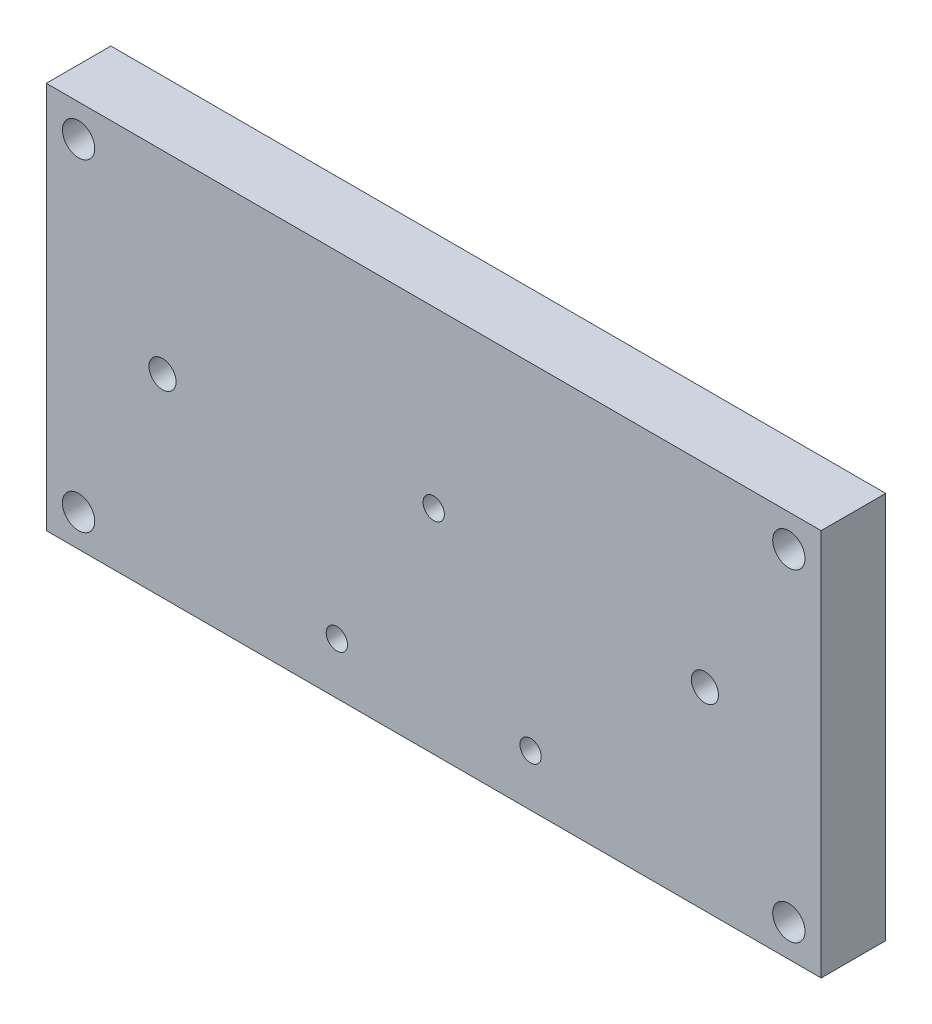
SolidWorks part; units mm, degrees
ref_plane "Ebene vorne" through (0, 0, 0) normal (0, 0, 1) x (1, 0, 0)
ref_plane "Ebene oben" through (0, 0, 0) normal (0, 1, 0) x (1, 0, 0)
ref_plane "Ebene rechts" through (0, 0, 0) normal (1, 0, 0) x (0, 0, -1)
sketch "Skizze1" plane through (0, 0, 0) normal (0, 0, 1) x (1, 0, 0)
  line L1 (-60, 30) -> (60, 30)
  line L2 (-60, 30) -> (-60, -30)
  line L3 (-60, -30) -> (60, -30)
  line L4 (60, 30) -> (60, -30)
  line L5 (-60, 30) -> (60, -30) construction
  line L6 (-60, -30) -> (60, 30) construction
  point P0 (0, 0)
  dimension "D1" = 120
  dimension "D2" = 60
extrude "Aufsatz-Linear austragen1" add sketch "Skizze1" along normal blind 10
sketch "Skizze2" plane through (0, 0, 10) normal (0, 0, 1) x (1, 0, 0)
  line L0 (-60, 30) -> (-60, -30) construction
  line L1 (55, -25) -> (-55, -25) construction
  line L2 (55, -25) -> (55, 25) construction
  line L3 (55, 25) -> (-55, 25) construction
  line L4 (-55, -25) -> (-55, 25) construction
  line L5 (55, -25) -> (-55, 25) construction
  line L6 (55, 25) -> (-55, -25) construction
  line L7 (-60, -30) -> (60, -30) construction
  point P0 (0, 0)
  point P7 (-55, 25)
  point P8 (55, 25)
  point P9 (55, -25)
  point P10 (-55, -25)
  dimension "D1" = 5
  dimension "D2" = 5
hole_wizard "M6 Gewindebohrung1" positions "Skizze3" profile "Skizze4" tap size "M6" standard "DIN" end condition through all
sketch "Skizze3" plane through (0, 0, 10) normal (0, 0, 1) x (1, 0, 0)
  point P0 (-55, -25)
  point P3 (-55, 25)
  point P6 (55, 25)
  point P9 (55, -25)
sketch "Skizze4" plane through (-55, -25, 10) normal (1, 0, 0) x (0, -1, 0)
  line L0 (0, 0) -> (0, 10)
  line L1 (0, 10) -> (2.5, 10)
  line L2 (2.5, 10) -> (2.5, 0)
  line L5 (2.5, 0) -> (0, 0)
  line L11 (0, -6.35) -> (0, 107.95) construction
  dimension "Bohrerdurchmesser" = 5
  dimension "Bohrungstiefe" = 10
cosmetic thread "Bohrungsgewinde1" parameters "D2"=6
cosmetic thread "Bohrungsgewinde2" parameters "D2"=6
cosmetic thread "Bohrungsgewinde3" parameters "D2"=6
cosmetic thread "Bohrungsgewinde4" parameters "D2"=6
hole_wizard "M5 Gewindebohrung1" positions "Skizze6" profile "Skizze7" tap size "M5" standard "DIN" end condition through all
sketch "Skizze6" plane through (0, 0, 10) normal (0, 0, 1) x (1, 0, 0)
  line L0 (0, 0) -> (0, 30) construction
  line L1 (60, 30) -> (-60, 30) construction
  line L3 (-60, 30) -> (-60, -30) construction
  point P0 (-42, 0)
  point P2 (42, 0)
  point P12 (0, 0)
  point P13 (0, 6.5163)
  point P14 (0, 0)
  point P15 (0, 0)
  dimension "D1" = 18
  dimension "D2" = 30
sketch "Skizze7" plane through (-42, 0, 10) normal (1, 0, 0) x (0, -1, 0)
  line L0 (0, 0) -> (0, 10)
  line L1 (0, 10) -> (2.1, 10)
  line L2 (2.1, 10) -> (2.1, 0)
  line L5 (2.1, 0) -> (0, 0)
  line L11 (0, -6.35) -> (0, 107.95) construction
  dimension "Bohrerdurchmesser" = 4.2
  dimension "Bohrungstiefe" = 10
cosmetic thread "Bohrungsgewinde5" parameters "D2"=5
cosmetic thread "Bohrungsgewinde6" parameters "D2"=5
hole_wizard "M4 Gewindebohrung1" positions "Skizze9" profile "Skizze10" tap size "M4" standard "DIN" end condition through all
sketch "Skizze9" plane through (0, 0, 10) normal (0, 0, 1) x (1, 0, 0)
  line L0 (0, 3) -> (0, -30) construction
  line L1 (-60, -30) -> (60, -30) construction
  point P0 (0, 3)
  point P12 (-15, -22)
  point P14 (15, -22)
  point P16 (0, 0)
  dimension "D1" = 3
  dimension "D2" = 30
  dimension "D3" = 25
sketch "Skizze10" plane through (0, 3, 10) normal (1, 0, 0) x (0, -1, 0)
  line L0 (0, 0) -> (0, 10)
  line L1 (0, 10) -> (1.65, 10)
  line L2 (1.65, 10) -> (1.65, 0)
  line L5 (1.65, 0) -> (0, 0)
  line L11 (0, -6.35) -> (0, 107.95) construction
  dimension "Bohrerdurchmesser" = 3.3
  dimension "Bohrungstiefe" = 10
cosmetic thread "Bohrungsgewinde7" parameters "D2"=4
cosmetic thread "Bohrungsgewinde8" parameters "D2"=4
cosmetic thread "Bohrungsgewinde9" parameters "D2"=4
